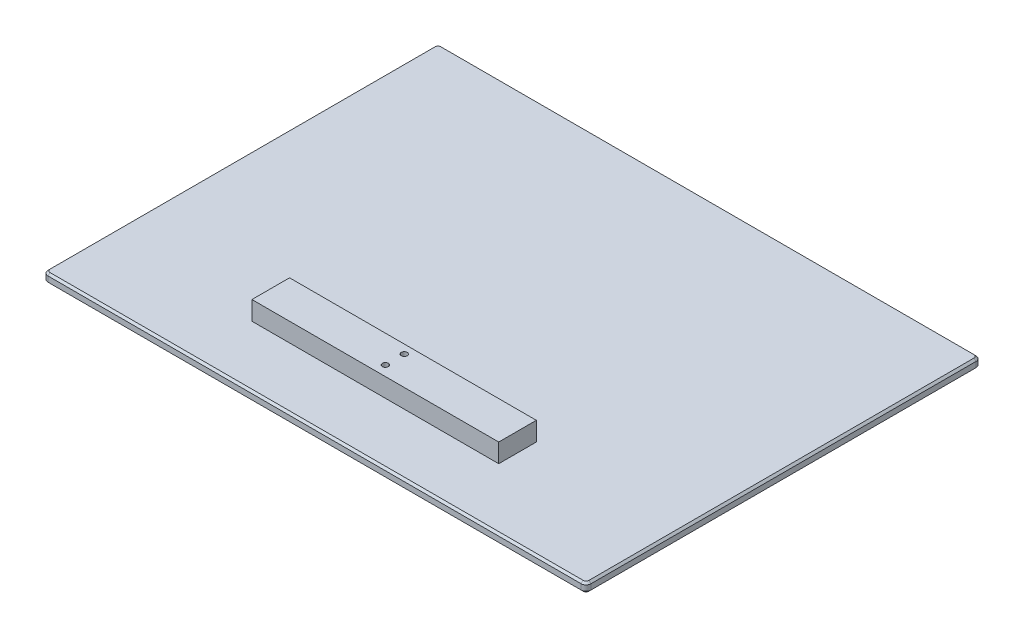
SolidWorks part; units mm, degrees
material "6061-T6 (SS)"
ref_plane "Front Plane" through (0, 0, 0) normal (0, 0, 1) x (1, 0, 0)
ref_plane "Top Plane" through (0, 0, 0) normal (0, 1, 0) x (1, 0, 0)
ref_plane "Right Plane" through (0, 0, 0) normal (1, 0, 0) x (0, 0, -1)
sketch "Sketch1" plane through (0, 0, 0) normal (0, 1, 0) x (1, 0, 0)
  line L1 (-275, 200) -> (275, 200)
  line L2 (-275, 200) -> (-275, -200)
  line L3 (-275, -200) -> (275, -200)
  line L4 (275, 200) -> (275, -200)
  line L5 (-275, 200) -> (275, -200) construction
  line L6 (-275, -200) -> (275, 200) construction
  point P0 (0, 0)
  dimension "D1" = 550
  dimension "D2" = 400
extrude "Boss-Extrude1" add sketch "Sketch1" along normal blind 9.525
sketch "Sketch2" plane through (0, 0, 0) normal (0, 1, 0) x (1, 0, 0)
  line L0 (0, 200) -> (0, -200) construction
  line L1 (275, 200) -> (-275, 200) construction
  line L2 (-275, -200) -> (275, -200) construction
  line L3 (-275, 0) -> (275, 0) construction
  line L4 (-275, 200) -> (-275, -200) construction
  line L5 (275, -200) -> (275, 200) construction
  line L6 (-275, -118.7) -> (275, -118.7) construction
  circle A0 centre (0, 9.55) radius 3 construction
  circle A1 centre (0, -9.55) radius 3 construction
  circle A2 centre (0, -109.15) radius 3 construction
  circle A3 centre (0, -128.25) radius 3 construction
  circle A4 centre (-30, -118.7) radius 3 construction
  circle A5 centre (30, -118.7) radius 3 construction
  dimension "D1" = 6
  dimension "D4" = 19.1
  dimension "D5" = 6
  dimension "D8" = 6
  dimension "D2" = 19.1
  dimension "D3" = 9.55
  dimension "D6" = 99.6
  dimension "D7" = 9.55
  dimension "D9" = 60
  dimension "D10" = 30
fillet "Fillet2" radius 5 4 edges at (-275, 4.7625, -200) (275, 4.7625, -200) (275, 4.7625, 200) (-275, 4.7625, 200)
chamfer "Chamfer1" distance 2 angle 45 8 edges at (0, 9.525, -200) (-273.5355, 9.525, -198.5355) (273.5355, 9.525, -198.5355) (-275, 9.525, 0) (275, 9.525, 0) (-273.5355, 9.525, 198.5355) (273.5355, 9.525, 198.5355) (0, 9.525, 200)
chamfer "Chamfer2" distance 2 angle 45 8 edges at (0, 0, -200) (-273.5355, 0, -198.5355) (273.5355, 0, -198.5355) (-275, 0, 0) (275, 0, 0) (-273.5355, 0, 198.5355) (273.5355, 0, 198.5355) (0, 0, 200)
sketch "Sketch3" plane through (0, 9.525, 0) normal (0, 1, 0) x (1, 0, 0)
  line L0 (0, 200) -> (0, -200) construction
  line L1 (-275, 0) -> (275, 0) construction
  line L2 (-275, -118.7) -> (275, -118.7) construction
  line L9 (-125, -100.35) -> (125, -100.35)
  line L10 (-125, -100.35) -> (-125, -138.45)
  line L11 (-125, -138.45) -> (125, -138.45)
  line L12 (125, -100.35) -> (125, -138.45)
  circle A0 centre (0, -109.15) radius 3
  circle A1 centre (0, -128.25) radius 3
  dimension "D1" = 6
  dimension "D2" = 38.1
  dimension "D3" = 250
  dimension "D4" = 8.8
  dimension "D5" = 125
extrude "Boss-Extrude2" add sketch "Sketch3" along normal blind 19.05
